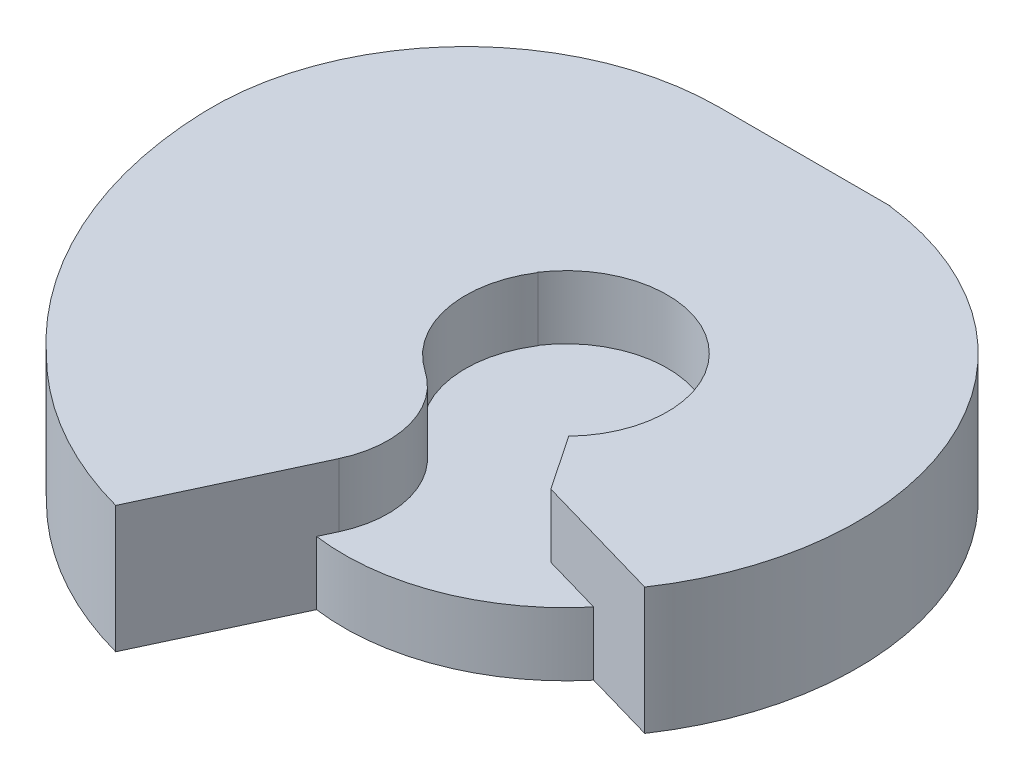
SolidWorks part; units mm, degrees
ref_plane "Front Plane" through (0, 0, 0) normal (0, 0, 1) x (1, 0, 0)
ref_plane "Top Plane" through (0, 0, 0) normal (0, 1, 0) x (1, 0, 0)
ref_plane "Right Plane" through (0, 0, 0) normal (1, 0, 0) x (0, 0, -1)
sketch "Sketch1" plane through (0, 0, 0) normal (0, 1, 0) x (1, 0, 0)
  circle A0 centre (0, 0) radius 8.89
  dimension "D1" = 17.78
extrude "Boss-Extrude1" add sketch "Sketch1" along normal blind 2.54
sketch "Sketch2" plane through (0, 0, 0) normal (0, -1, 0) x (1, 0, 0)
  line L12 (-5.4702, -11.6162) -> (1.3705, -11.6133)
  line L13 (1.3705, -11.6133) -> (1.3705, -11.6033)
  line L14 (9.6894, 6.5292) -> (4.4093, 5.0119)
  line L15 (4.4093, 5.0119) -> (2.9301, 2.8161)
  line L16 (-3.3887, -2.2435) -> (-3.3669, -2.2454)
  line L17 (-0.8967, 8.1978) -> (-3.7436, 14.2961)
  line L18 (-5.4702, -11.6162) -> (1.3705, -11.6133)
  line L19 (1.3705, -11.6133) -> (1.3705, -11.6033)
  line L20 (9.6894, 6.5292) -> (4.4093, 5.0119)
  line L21 (4.4093, 5.0119) -> (2.9301, 2.8161)
  line L22 (-3.3887, -2.2435) -> (-3.3669, -2.2454)
  line L23 (-0.8967, 8.1978) -> (-3.7436, 14.2961)
  arc A14 (-10.3107, 10.5078) -> (-15.6293, -1.132) centre (0.9236, -1.6604) ccw
  arc A15 (-15.6293, -1.132) -> (-5.4702, -11.6162) centre (-5.4744, -1.4562) ccw
  arc A16 (1.3705, -11.6033) -> (9.6894, 6.5292) centre (0, 0) ccw
  arc A17 (-3.3887, -2.2435) -> (2.9301, 2.8161) centre (0, 0) ccw
  arc A18 (-2.2075, 3.435) -> (-3.3669, -2.2454) centre (0.127, 0.0001) ccw
  arc A19 (-2.2075, 3.435) -> (-0.8967, 8.1978) centre (-4.3491, 6.5862) ccw
  arc A20 (-3.7436, 14.2961) -> (-10.3107, 10.5078) centre (0.127, 0.0001) ccw
  arc A21 (-10.3107, 10.5078) -> (-15.6293, -1.132) centre (0.9236, -1.6604) ccw
  arc A22 (-15.6293, -1.132) -> (-5.4702, -11.6162) centre (-5.4744, -1.4562) ccw
  arc A23 (1.3705, -11.6033) -> (9.6894, 6.5292) centre (0, 0) ccw
  arc A24 (-3.3887, -2.2435) -> (2.9301, 2.8161) centre (0, 0) ccw
  arc A25 (-2.2075, 3.435) -> (-3.3669, -2.2454) centre (0.127, 0.0001) ccw
  arc A26 (-2.2075, 3.435) -> (-0.8967, 8.1978) centre (-4.3491, 6.5862) ccw
  arc A27 (-3.7436, 14.2961) -> (-10.3107, 10.5078) centre (0.127, 0.0001) ccw
  dimension "D1" = 2.54
extrude "Boss-Extrude2" add sketch "Sketch2" against normal blind 5.08
